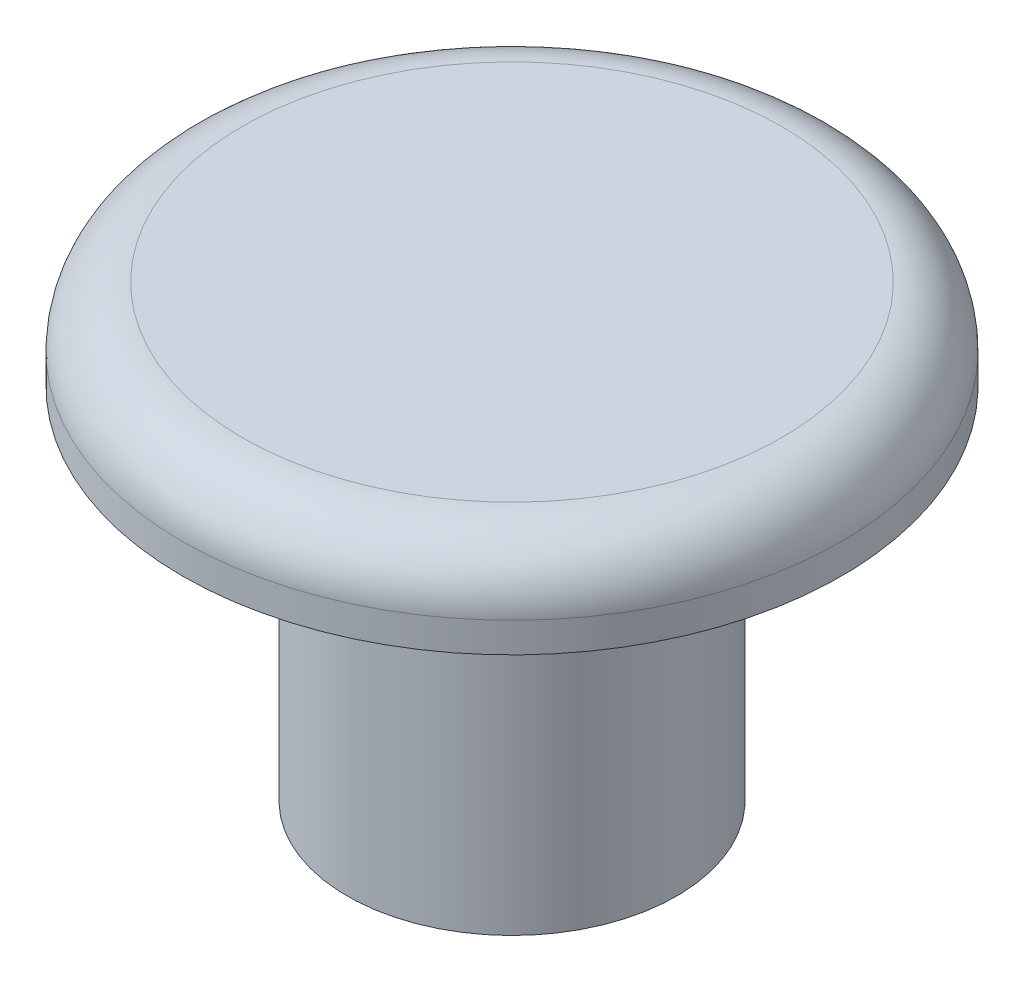
SolidWorks part; units mm, degrees
ref_plane "Front Plane" through (0, 0, 0) normal (0, 0, 1) x (1, 0, 0)
ref_plane "Top Plane" through (0, 0, 0) normal (0, 1, 0) x (1, 0, 0)
ref_plane "Right Plane" through (0, 0, 0) normal (1, 0, 0) x (0, 0, -1)
sketch "Sketch2" plane through (0, 0, 0) normal (0, 1, 0) x (1, 0, 0)
  circle A0 centre (0, 0) radius 11
  dimension "D1" = 22
extrude "Boss-Extrude1" add sketch "Sketch2" along normal blind 3 contours A0
fillet "Fillet1" radius 2 1 edges at (0, 3, 11)
sketch "Sketch3" plane through (0, 0, 0) normal (0, -1, 0) x (1, 0, 0)
  circle A0 centre (0, 0) radius 5.5
  dimension "D1" = 11
extrude "Boss-Extrude2" add sketch "Sketch3" along normal blind 12
